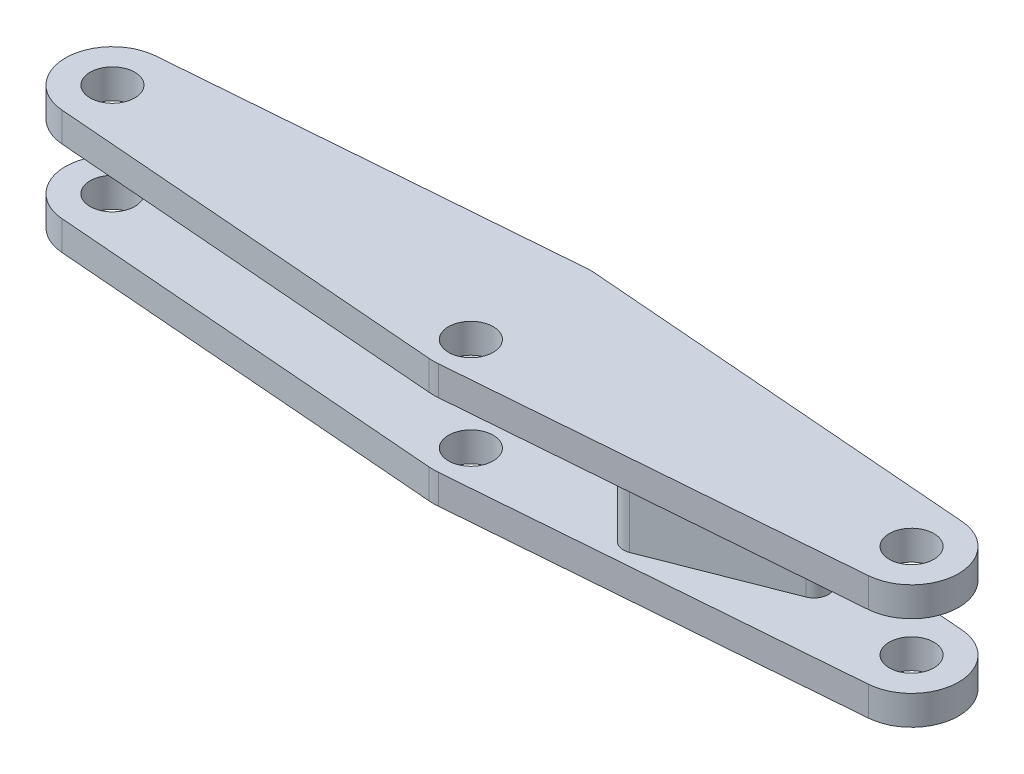
SolidWorks part; units mm, degrees
ref_plane "Front Plane" through (0, 0, 0) normal (0, 0, 1) x (1, 0, 0)
ref_plane "Top Plane" through (0, 0, 0) normal (0, 1, 0) x (1, 0, 0)
ref_plane "Right Plane" through (0, 0, 0) normal (1, 0, 0) x (0, 0, -1)
sketch "Sketch1" plane through (0, 0, 0) normal (0, 1, 0) x (1, 0, 0)
  line L0 (-0.985, 16.6721) -> (-85.788, 9.9689)
  line L1 (0.985, -16.6721) -> (85.788, -9.9689)
  line L2 (0, 0) -> (0, 16.75) construction
  line L3 (0, 16.75) -> (0, -23.25) construction
  line L4 (-85, 0) -> (-80.25, 0) construction
  line L5 (-0.985, -16.6721) -> (-85.788, -9.9689)
  line L6 (0.985, 16.6721) -> (85.788, 9.9689)
  line L7 (-75, 0) -> (85, 0) construction
  circle A0 centre (-85, 0) radius 4.75
  arc A1 (-85.788, 9.9689) -> (-85.788, -9.9689) centre (-85, 0) ccw
  arc A2 (85.788, 9.9689) -> (85.788, -9.9689) centre (85, 0) cw
  circle A3 centre (85, 0) radius 4.75
  arc A4 (0.985, -16.6721) -> (-0.985, -16.6721) centre (0, -4.211) cw
  arc A5 (-0.985, 16.6721) -> (0.985, 16.6721) centre (0, 4.211) cw
  circle A6 centre (0, -8.75) radius 4.75
  point P17 (0, -23.25)
  point P23 (0, 0)
  dimension "D3" = 9.5
  dimension "D4" = 20
  dimension "D6" = 12.5
  dimension "D8" = 9.5
  dimension "D1" = 170
  dimension "D2" = 16.75
  dimension "D5" = 40
  dimension "D7" = 8.75
  dimension "D9" = 40
extrude "Boss-Extrude1" add sketch "Sketch1" along normal mid plane 26.25
ref_plane "Plane1" through (0, 0, 17) normal (0, 0, 1) x (1, 0, 0)
sketch "Sketch2" plane through (0, 0, 17) normal (0, 0, 1) x (1, 0, 0)
  line L0 (-95, 13.125) -> (-95, -13.125) construction
  line L1 (95, 6.875) -> (-95, 6.875)
  line L2 (95, 6.875) -> (95, -6.875)
  line L3 (95, -6.875) -> (-95, -6.875)
  line L4 (-95, 6.875) -> (-95, -6.875)
  line L5 (95, 6.875) -> (-95, -6.875) construction
  line L6 (95, -6.875) -> (-95, 6.875) construction
  line L7 (-85.788, 13.125) -> (-95, 13.125) construction
  point P0 (0, 0)
  dimension "D1" = 6.25
extrude "Cut-Extrude1" cut sketch "Sketch2" against normal through all
ref_plane "Plane2" through (0, 0, 0) normal (0, 1, 0) x (1, 0, 0)
sketch "Sketch3" plane through (0, 0, 0) normal (0, 1, 0) x (1, 0, 0)
  line L0 (0, 0) -> (63.9254, 0) construction
  line L1 (6.1599, 2.25) -> (62.0072, 2.25) construction
  line L2 (35, -8.3146) -> (62.0072, 2.25) construction
  line L3 (33.9071, -5.5207) -> (60.9143, 5.0439)
  line L4 (36.0929, -11.1084) -> (63.1001, -0.5439)
  arc A0 (33.9071, -5.5207) -> (36.0929, -11.1084) centre (35, -8.3146) ccw
  arc A1 (63.1001, -0.5439) -> (60.9143, 5.0439) centre (62.0072, 2.25) ccw
  point P6 (48.5036, -3.0323)
  dimension "D2" = 29
  dimension "D3" = 3
  dimension "D1" = 35
  dimension "D4" = 8.3146
  dimension "D5" = 2.25
extrude "Boss-Extrude4" add sketch "Sketch3" along normal blind 6.875 and the other way blind 6.875
